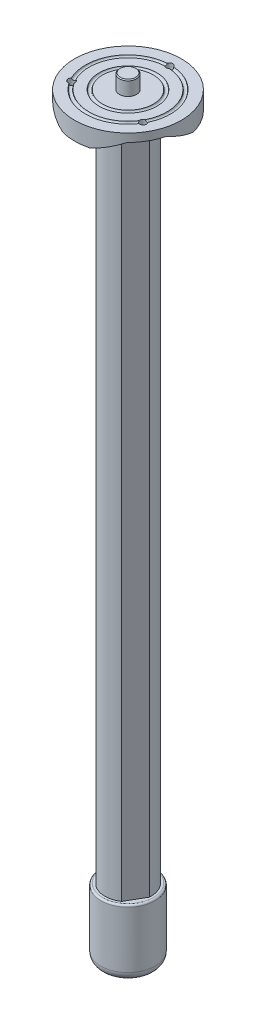
SolidWorks part; units mm, degrees
ref_plane "Front Plane" through (0, 0, 0) normal (0, 0, 1) x (1, 0, 0)
ref_plane "Top Plane" through (0, 0, 0) normal (0, 1, 0) x (1, 0, 0)
ref_plane "Right Plane" through (0, 0, 0) normal (1, 0, 0) x (0, 0, -1)
sketch "Sketch2" plane through (0, 0, 0) normal (0, 1, 0) x (1, 0, 0)
  line L0 (-5.6461, 11.6544) -> (5.6461, 11.6544) construction
  line L1 (12.916, -0.9375) -> (7.2699, -10.7168) construction
  line L2 (-5.6, 11.4544) -> (5.6, 11.4544)
  line L3 (12.7198, -0.8774) -> (7.1198, -10.5769)
  line L4 (-7.1198, -10.5769) -> (-12.7198, -0.8774)
  line L5 (-7.2699, -10.7168) -> (-12.916, -0.9375) construction
  arc A0 (-5.6, 11.4544) -> (-12.7198, -0.8774) centre (0, 0) ccw
  arc A1 (-7.1198, -10.5769) -> (7.1198, -10.5769) centre (0, 0) ccw
  arc A2 (12.7198, -0.8774) -> (5.6, 11.4544) centre (0, 0) ccw
  arc A3 (12.916, -0.9375) -> (5.6461, 11.6544) centre (0, 0) ccw construction
  arc A4 (-7.2699, -10.7168) -> (7.2699, -10.7168) centre (0, 0) ccw construction
  arc A5 (-5.6461, 11.6544) -> (-12.916, -0.9375) centre (0, 0) ccw construction
  dimension "D1" = 0.2
extrude "Extrude1" add sketch "Sketch2" along normal mid plane 370
sketch "Sketch3" plane through (0, 185, 0) normal (0, 1, 0) x (1, 0, 0)
  circle A0 centre (0, 0) radius 29.5
  dimension "D1" = 59
extrude "Extrude2" add sketch "Sketch3" along normal blind 10 separate body
ref_plane "Plane1" through (0, 0, -35) normal (0, 0, 1) x (1, 0, 0)
sketch "Sketch7" plane through (0, 0, 0) normal (0, 0, 1) x (1, 0, 0)
  line L0 (0, 203.8228) -> (0, 175.1069) construction
  line L1 (29.5, 195) -> (-29.5, 195) construction
  circle A0 centre (15, 195) radius 1
  circle A1 centre (22.5, 195) radius 1
  dimension "D1" = 30
  dimension "D2" = 45
  dimension "D3" = 2
revolve "Cut-Revolve1" cut sketch "Sketch7" angle 360 about L0
sketch "Sketch6" plane through (0, 185, 0) normal (0, -1, 0) x (1, 0, 0)
  circle A2 centre (0, 0) radius 25.5
  circle A3 centre (0, 0) radius 25.5
  circle A4 centre (0, 0) radius 29.5
  circle A5 centre (0, 0) radius 29.5
  dimension "D1" = 4
  dimension "D2" = 0
extrude "Extrude4" cut sketch "Sketch6" against normal blind 5.5 flip side to cut
sketch "Sketch4" plane through (0, 0, -35) normal (0, 0, 1) x (1, 0, 0)
  line L0 (0, 203.7466) -> (0, 160.4159) construction
  line L1 (8, 190.5) -> (-8, 190.5)
  line L2 (-8, 190.5) -> (-21, 185)
  line L3 (-29.5, 185) -> (29.5, 185) construction
  line L4 (29.5, 195) -> (-29.5, 195) construction
  line L5 (-21, 185) -> (21, 185)
  line L6 (8, 190.5) -> (21, 185)
  point P12 (0, 185)
  point P13 (0, 190.5)
  dimension "D1" = 16
  dimension "D2" = 4.5
  dimension "D3" = 42
  dimension "D4" = 5.5
extrude "Extrude3" cut sketch "Sketch4" along normal blind 23
pattern_circular "CirPattern1" count 3 over 360 about axis through (0, 0, 0) along (0, 1, 0) of "Extrude3"
sketch "Sketch8" plane through (0, 195, 0) normal (0, 1, 0) x (1, 0, 0)
  circle A0 centre (0, 0) radius 4.7625
  dimension "D1" = 9.525
extrude "Extrude5" add sketch "Sketch8" along normal blind 8 separate body
chamfer "Chamfer1" distance 0.5 angle 45 1 edges at (0, 203, 4.7625)
sketch "Sketch9" plane through (0, 185, 0) normal (0, 1, 0) x (1, 0, 0)
  line L3 (-12.7198, -0.8774) -> (-7.1198, -10.5769)
  line L4 (7.1198, -10.5769) -> (12.7198, -0.8774)
  line L5 (5.6, 11.4544) -> (-5.6, 11.4544)
  line L6 (-12.7198, -0.8774) -> (-7.1198, -10.5769)
  line L7 (7.1198, -10.5769) -> (12.7198, -0.8774)
  line L8 (5.6, 11.4544) -> (-5.6, 11.4544)
  arc A3 (-5.6, 11.4544) -> (-12.7198, -0.8774) centre (0, 0) ccw
  arc A4 (-7.1198, -10.5769) -> (7.1198, -10.5769) centre (0, 0) ccw
  arc A5 (12.7198, -0.8774) -> (5.6, 11.4544) centre (0, 0) ccw
  arc A6 (-5.6, 11.4544) -> (-12.7198, -0.8774) centre (0, 0) ccw
  arc A7 (-7.1198, -10.5769) -> (7.1198, -10.5769) centre (0, 0) ccw
  arc A8 (12.7198, -0.8774) -> (5.6, 11.4544) centre (0, 0) ccw
  dimension "D1" = 0
extrude "Extrude6" add sketch "Sketch9" along normal blind 8 separate body
sketch "Sketch10" plane through (0, 0, 0) normal (0, 0, 1) x (1, 0, 0)
  line L0 (0, -169.776) -> (0, -233.5826) construction
  line L1 (15, -185) -> (15, -220)
  line L2 (-7.1198, -185) -> (7.1198, -185) construction
  line L3 (0, -185) -> (15, -185)
  line L4 (-8.9046, -225) -> (11.9553, -225) construction
  line L5 (0, -185) -> (0, -225)
  arc A0 (0, -225) -> (15, -220) centre (0, -200) ccw
  dimension "D1" = 35
  dimension "D2" = 30
  dimension "D3" = 40
revolve "Revolve1" add sketch "Sketch10" angle 360 about L5
fillet "Fillet1" radius 5 1 edges at (-15, -220, 0)
fillet "Fillet2" radius 1 1 edges at (-15, -185, 0)
combine bodies "Combine1" operation type add bodies to combine 111 101
hole_wizard "#10-24 Tapped Hole1" positions "Sketch11" profile "Sketch13" tap size "#10-24" standard "ANSI Inch" end condition through all
sketch "Sketch11" plane through (0, 195, 0) normal (0, 1, 0) x (1, 0, 0)
  line L0 (0, 22.86) -> (19.7973, -11.43) construction
  line L1 (19.7973, -11.43) -> (-19.7973, -11.43) construction
  line L2 (-19.7973, -11.43) -> (0, 22.86) construction
  line L4 (-19.7973, -11.43) -> (0, 0) construction
  line L6 (19.7973, -11.43) -> (0, 0) construction
  line L8 (0, 22.86) -> (0, 0) construction
  circle A0 centre (0, 0) radius 4.2625 construction
  point P1 (0, 22.86)
  point P2 (19.7973, -11.43)
  point P4 (-19.7973, -11.43)
  dimension "D1" = 22.86
sketch "Sketch13" plane through (0, 195, -22.86) normal (1, 0, 0) x (0, 0, 1)
  line L0 (0, 0) -> (0, 420)
  line L1 (0, 420) -> (1.8986, 420)
  line L2 (1.8986, 420) -> (1.8986, 0)
  line L5 (1.8986, 0) -> (0, 0)
  line L11 (0, -6.35) -> (0, 107.95) construction
  dimension "Thread Major Dia." = 3.7973
  dimension "Thru Tap Drill Depth" = 420
